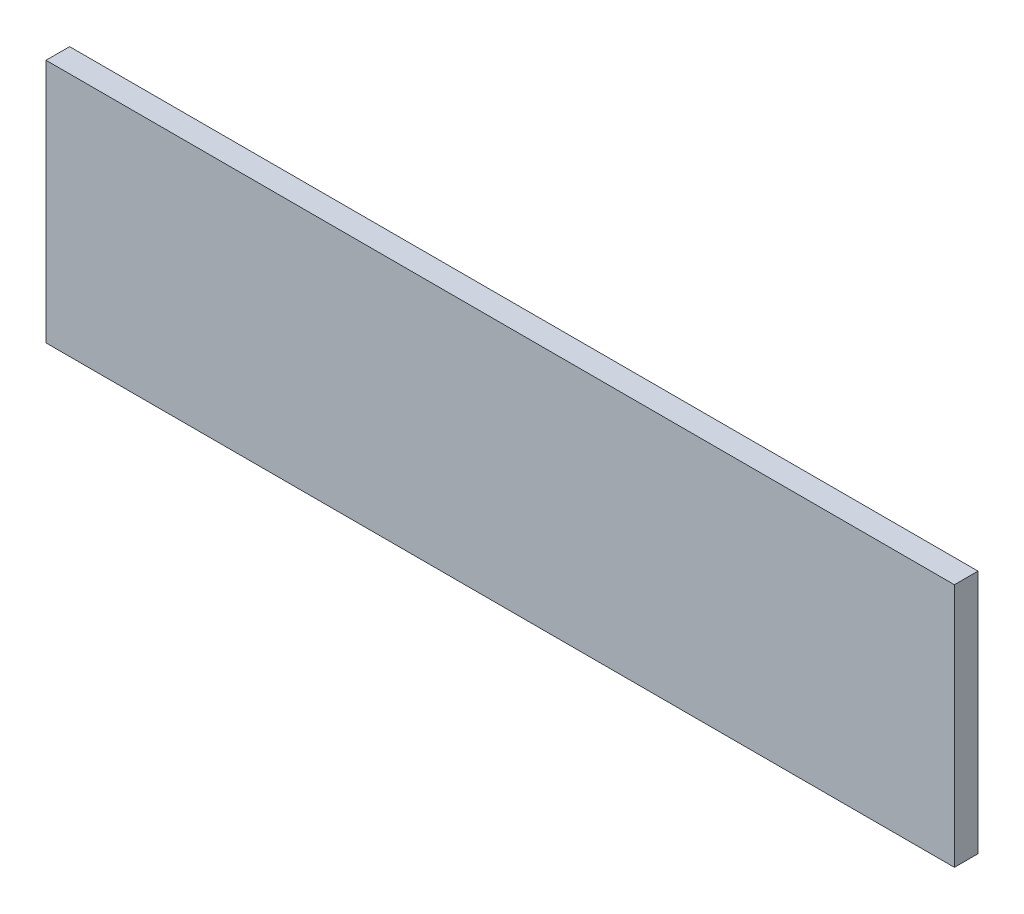
SolidWorks part; units mm, degrees
ref_plane "Plan de face" through (0, 0, 0) normal (0, 0, 1) x (1, 0, 0)
ref_plane "Plan de dessus" through (0, 0, 0) normal (0, 1, 0) x (1, 0, 0)
ref_plane "Plan de droite" through (0, 0, 0) normal (1, 0, 0) x (0, 0, -1)
sketch "Esquisse1" plane through (0, 0, 0) normal (0, 0, 1) x (1, 0, 0)
  line L1 (0, 0) -> (308, 0)
  line L2 (0, 0) -> (0, 83)
  line L3 (0, 83) -> (308, 83)
  line L4 (308, 0) -> (308, 83)
  dimension "D1" = 308
  dimension "D2" = 83
extrude "Extrusion1" add sketch "Esquisse1" against normal blind 8
